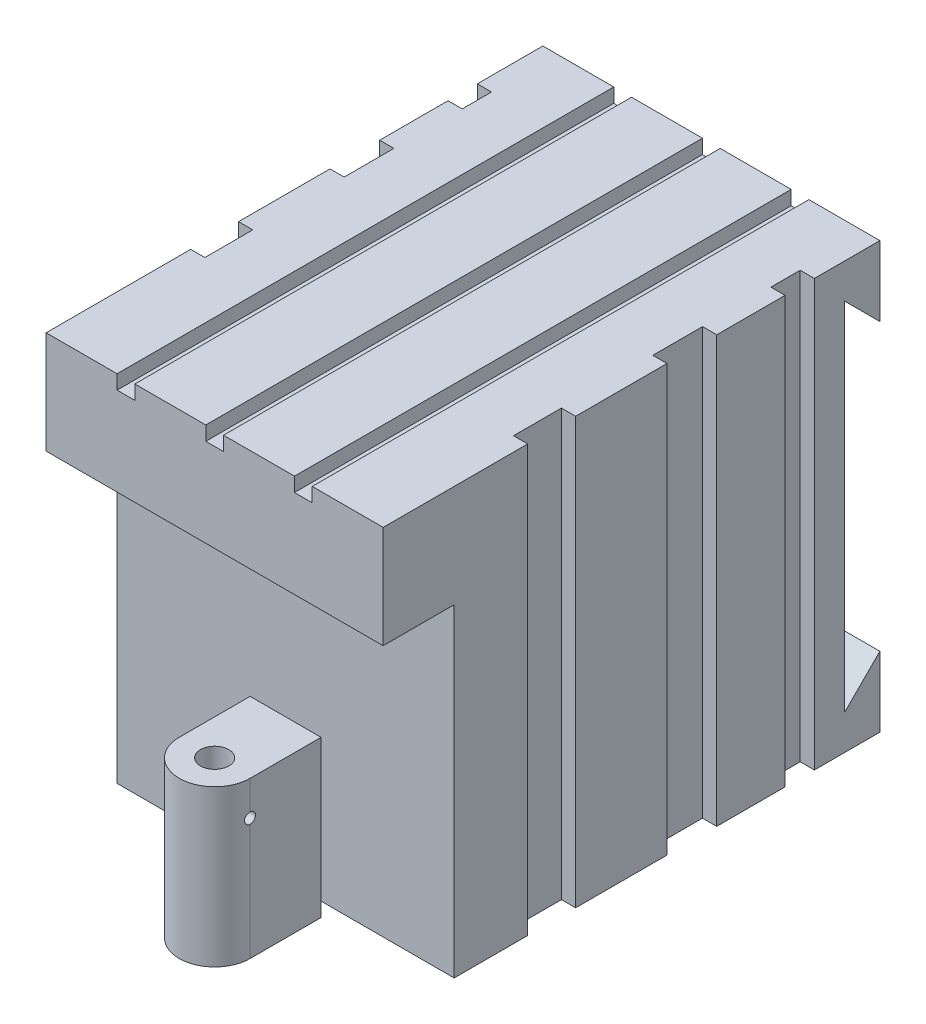
SolidWorks part; units mm, degrees
ref_plane "Front Plane" through (0, 0, 0) normal (0, 0, 1) x (1, 0, 0)
ref_plane "Top Plane" through (0, 0, 0) normal (0, 1, 0) x (1, 0, 0)
ref_plane "Right Plane" through (0, 0, 0) normal (1, 0, 0) x (0, 0, -1)
sketch "Sketch1" plane through (0, 0, 0) normal (0, 1, 0) x (1, 0, 0)
  line L1 (-45.8641, 19.0121) -> (4.1359, 19.0121)
  line L2 (-45.8641, 19.0121) -> (-45.8641, -50.9879)
  line L3 (-45.8641, -50.9879) -> (4.1359, -50.9879)
  line L4 (4.1359, 19.0121) -> (4.1359, -50.9879)
  dimension "D1" = 50
  dimension "D2" = 70
extrude "Boss-Extrude1" add sketch "Sketch1" along normal blind 60
sketch "Sketch2" plane through (4.1359, 0, 0) normal (1, 0, 0) x (0, 0, -1)
  line L0 (14.0121, 55.1221) -> (14.0121, 4.8779)
  line L1 (19.0121, 60) -> (19.0121, 0) construction
  line L2 (19.0121, 55.1221) -> (14.0121, 55.1221)
  line L3 (19.0121, 55.1221) -> (19.0121, 50.1221)
  line L5 (14.0121, 4.8779) -> (19.0121, 9.8779)
  line L6 (14.0121, 55.1221) -> (19.0121, 50.1221)
  line L7 (19.0121, 4.8779) -> (19.0121, 9.8779)
  line L8 (19.0121, 4.8779) -> (14.0121, 4.8779)
  line M2 (19.0121, 0) -> (19.0121, 60)
extrude "Cut-Extrude1" cut sketch "Sketch2" against normal blind 60 contours L6 L0 L5 M2
sketch "Sketch4" plane through (0, 0, 50.9879) normal (0, 0, 1) x (1, 0, 0)
  line L1 (-45.8641, 60) -> (4.1359, 60) construction
  line L3 (-45.8641, 60) -> (-35.8641, 60)
  line L4 (-35.8641, 60) -> (-35.8641, 58)
  line L5 (-35.8641, 58) -> (-33.3641, 58)
  line L6 (-33.3641, 58) -> (-33.3641, 60)
  line L7 (-33.3641, 60) -> (-23.3641, 60)
  line L8 (-23.3641, 58) -> (-23.3641, 60)
  line L9 (-10.8641, 60) -> (-20.8641, 60)
  line L10 (-20.8641, 60) -> (-20.8641, 58)
  line L11 (-20.8641, 58) -> (-23.3641, 58)
  line L13 (1.6359, 60) -> (-8.3641, 60)
  line L14 (-8.3641, 58) -> (-8.3641, 60)
  line L15 (-10.8641, 58) -> (-8.3641, 58)
  line L16 (-10.8641, 60) -> (-10.8641, 58)
  line L17 (1.6359, 60) -> (1.6359, 0)
  line L18 (-45.8641, 0) -> (4.1359, 0) construction
  line L19 (1.6359, 0) -> (4.1359, 0)
  line L20 (4.1359, 0) -> (4.1359, 60)
  line L21 (4.1359, 60) -> (1.6359, 60)
  line M1 (-45.8641, 0) -> (4.1359, 0)
  line M2 (4.1359, 0) -> (4.1359, 60)
  line M3 (4.1359, 60) -> (-45.8641, 60)
extrude "Cut-Extrude2" cut sketch "Sketch4" against normal blind 95 contours L5 L6 L4 M3 | L11 L10 L8 M3 | L16 L15 L14 M3 | L17 M3 M1 M2
sketch "Sketch7" plane through (0, 0, 50.9879) normal (0, 0, 1) x (1, 0, 0)
  line L0 (1.6359, 60) -> (1.6359, 0) construction
  line L1 (-45.8641, 0) -> (1.6359, 0)
  line L2 (-45.8641, 0) -> (-45.8641, 45.5542)
  line L3 (-45.8641, 45.5542) -> (1.6359, 45.5542)
  line L4 (1.6359, 0) -> (1.6359, 45.5542)
extrude "Cut-Extrude3" cut sketch "Sketch7" against normal blind 10
sketch "Sketch8" plane through (0, 0, 0) normal (0, -1, 0) x (1, 0, 0)
  line L0 (-17.1141, 40.9879) -> (-27.1141, 40.9879)
  line L2 (1.6359, 40.9879) -> (-45.8641, 40.9879) construction
  line L3 (-27.1141, 40.9879) -> (-27.1141, 50.9879)
  line L4 (1.6359, 50.9879) -> (-45.8641, 50.9879) construction
  line L6 (-17.1141, 40.9879) -> (-17.1141, 50.9879)
  arc A0 (-27.1141, 50.9879) -> (-17.1141, 50.9879) centre (-22.1141, 50.9879) cw
  circle A1 centre (-22.1141, 50.9879) radius 2
extrude "Boss-Extrude2" add sketch "Sketch8" against normal blind 20 and the other way blind 2
sketch "Sketch9" plane through (1.6359, 0, 0) normal (1, 0, 0) x (0, 0, -1)
  line L0 (19.0121, 60) -> (-50.9879, 60) construction
  line L1 (-30.6206, 60) -> (-23.8663, 60)
  line L2 (-30.6206, 60) -> (-30.6206, 0)
  line L3 (-30.6206, 0) -> (-23.8663, 0)
  line L4 (-23.8663, 60) -> (-23.8663, 0)
  line L5 (19.0121, 0) -> (-40.9879, 0) construction
  line L7 (-10.9879, 60) -> (-3.9788, 60)
  line L8 (-10.9879, 60) -> (-10.9879, 0)
  line L9 (-10.9879, 0) -> (-3.9788, 0)
  line L10 (-3.9788, 60) -> (-3.9788, 0)
  line L11 (5.6523, 60) -> (9.7799, 60)
  line L12 (5.6523, 60) -> (5.6523, 0)
  line L13 (5.6523, 0) -> (9.7799, 0)
  line L14 (9.7799, 60) -> (9.7799, 0)
extrude "Cut-Extrude4" cut sketch "Sketch9" against normal blind 2
sketch "Sketch10" plane through (0, 60, 0) normal (0, 1, 0) x (1, 0, 0)
  line L0 (-45.8641, 9.7799) -> (-45.8641, 5.6523)
  line L1 (-45.8641, 19.0121) -> (-45.8641, -50.9879) construction
  line L2 (-45.8641, -3.9788) -> (-45.8641, -10.9879)
  line L3 (-45.8641, -23.8663) -> (-45.8641, -30.6206)
  line L16 (-43.8641, -30.6206) -> (-45.8641, -30.6206)
  line L17 (-43.8641, -23.8663) -> (-43.8641, -30.6206)
  line L18 (-45.8641, -23.8663) -> (-43.8641, -23.8663)
  line L19 (-43.8641, -10.9879) -> (-45.8641, -10.9879)
  line L20 (-43.8641, -3.9788) -> (-43.8641, -10.9879)
  line L21 (-45.8641, -3.9788) -> (-43.8641, -3.9788)
  line L22 (-43.8641, 5.6523) -> (-45.8641, 5.6523)
  line L23 (-43.8641, 9.7799) -> (-43.8641, 5.6523)
  line L24 (-45.8641, 9.7799) -> (-43.8641, 9.7799)
extrude "Cut-Extrude5" cut sketch "Sketch10" against normal blind 71
sketch "Sketch11" plane through (-17.1141, 0, 0) normal (1, 0, 0) x (0, 0, -1)
  line L0 (-50.9879, -2) -> (-50.9879, 20) construction
  circle A0 centre (-50.9879, 15.1462) radius 0.75
  dimension "D1" = 1.5
extrude "Cut-Extrude6" cut sketch "Sketch11" against normal blind 4
sketch "Sketch12" plane through (0, 60, 0) normal (0, 1, 0) x (1, 0, 0)
